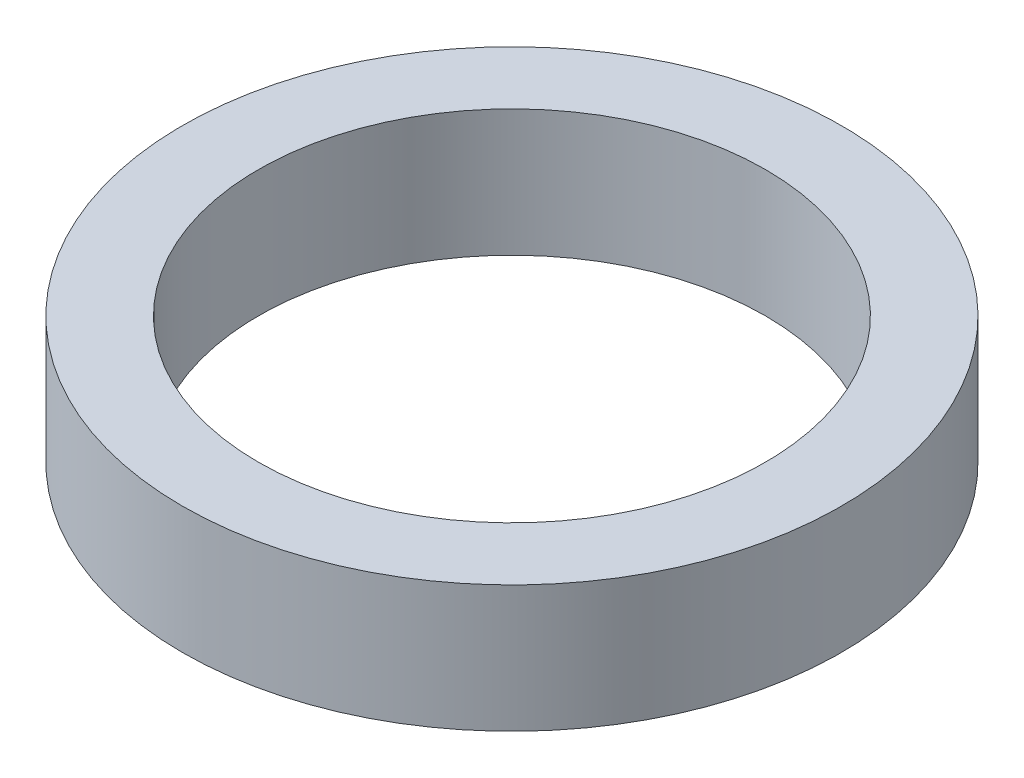
SolidWorks part; units mm, degrees
ref_plane "Front Plane" through (0, 0, 0) normal (0, 0, 1) x (1, 0, 0)
ref_plane "Top Plane" through (0, 0, 0) normal (0, 1, 0) x (1, 0, 0)
ref_plane "Right Plane" through (0, 0, 0) normal (1, 0, 0) x (0, 0, -1)
sketch "Sketch1" plane through (0, 0, 0) normal (0, 1, 0) x (1, 0, 0)
  circle A0 centre (0, 0) radius 2
  circle A1 centre (0, 0) radius 2.6
  dimension "D1" = 4
  dimension "D2" = 5.2
extrude "Boss-Extrude1" add sketch "Sketch1" along normal blind 1
